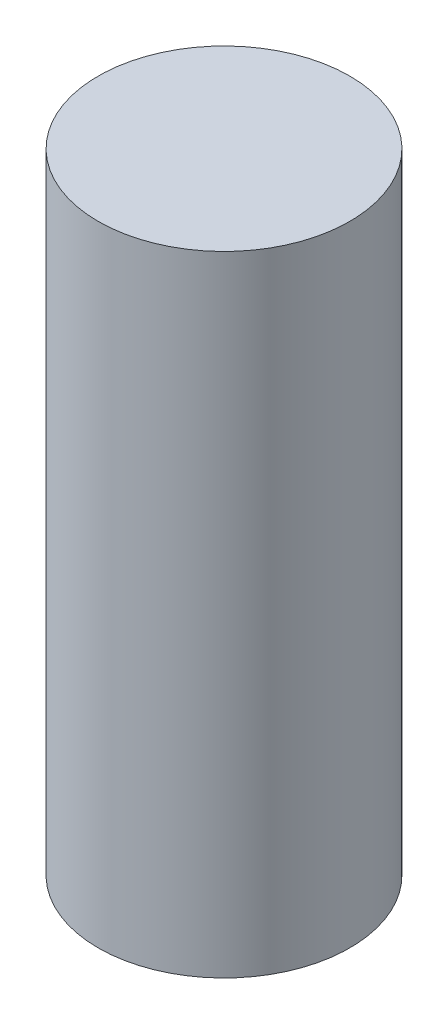
SolidWorks part; units mm, degrees
ref_plane "Front Plane" through (0, 0, 0) normal (0, 0, 1) x (1, 0, 0)
ref_plane "Top Plane" through (0, 0, 0) normal (0, 1, 0) x (1, 0, 0)
ref_plane "Right Plane" through (0, 0, 0) normal (1, 0, 0) x (0, 0, -1)
sketch "Sketch1" plane through (0, 0, 0) normal (0, 0, 1) x (1, 0, 0)
  line L0 (0, 0) -> (0, 100) construction
  line L2 (0, 0) -> (20, 0)
  line L3 (0, 0) -> (0, 100)
  line L4 (0, 100) -> (20, 100)
  line L5 (20, 0) -> (20, 100)
  dimension "D1" = 100
  dimension "D2" = 20
revolve "Revolve1" add sketch "Sketch1" angle 360 about L0
